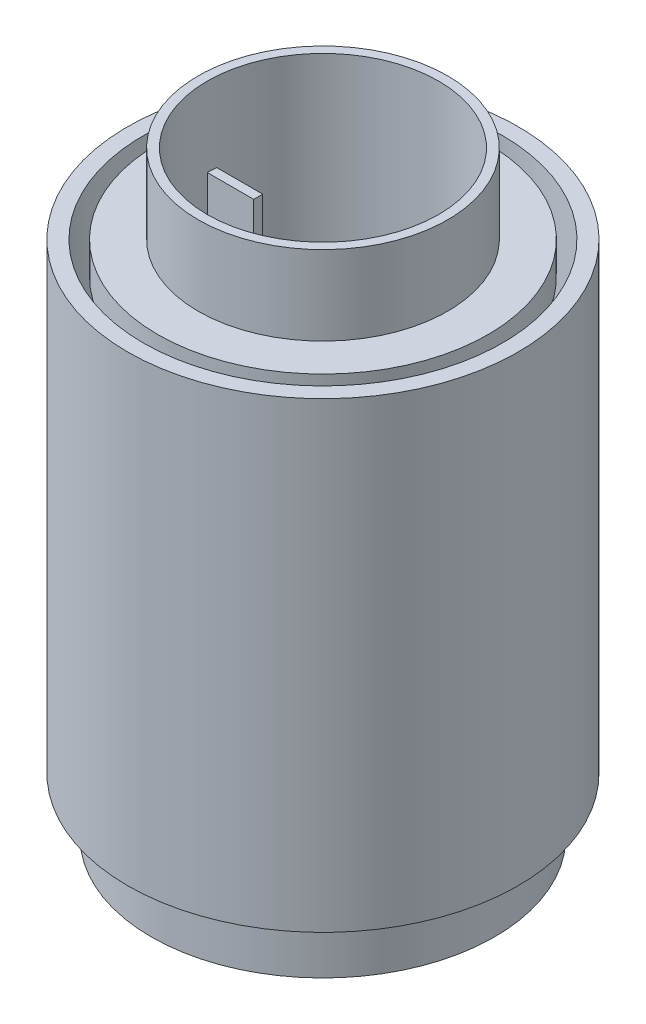
SolidWorks part; units mm, degrees
ref_plane "Alzado" through (0, 0, 0) normal (0, 0, 1) x (1, 0, 0)
ref_plane "Planta" through (0, 0, 0) normal (0, 1, 0) x (1, 0, 0)
ref_plane "Vista lateral" through (0, 0, 0) normal (1, 0, 0) x (0, 0, -1)
sketch "Croquis1" plane through (0, 0, 0) normal (0, 1, 0) x (1, 0, 0)
  circle A0 centre (0, 0) radius 25
  circle A1 centre (0, 0) radius 17.6776
  dimension "D1" = 50
extrude "Saliente-Extruir1" add sketch "Croquis1" along normal blind 5
sketch "Croquis3" plane through (0, 5, 0) normal (0, 1, 0) x (1, 0, 0)
  circle A0 centre (0, 0) radius 17.518
  circle A1 centre (0, 0) radius 25 construction
  circle A2 centre (0, 0) radius 17.6443
  dimension "D1" = 35.0359
extrude "Saliente-Extruir3" add sketch "Croquis3" against normal blind 70 separate body
sketch "Croquis5" plane through (0, 0, 0) normal (0, -1, 0) x (-1, 0, 0)
  circle A0 centre (0, 0) radius 17.518
  circle A1 centre (0, 0) radius 25.75
  circle A2 centre (0, 0) radius 25 construction
  dimension "D1" = 35.0359
  dimension "D2" = 51.5
ref_plane "Plano1" through (0, -65, 0) normal (0, 1, 0) x (1, 0, 0)
sketch "Croquis6" plane through (0, -65, 0) normal (0, 1, 0) x (1, 0, 0)
  circle A0 centre (0, 0) radius 17.518
  circle A1 centre (0, 0) radius 26
  dimension "D1" = 35.0359
  dimension "D2" = 52
extrude "Saliente-Extruir5" add sketch "Croquis6" against normal blind 8.5
sketch "Croquis7" plane through (0, -65, 0) normal (0, 1, 0) x (1, 0, 0)
  line L0 (17.4651, 1.3604) -> (10.4841, 1.3604)
  line L1 (10.4841, 1.3604) -> (10.4841, 0)
  line L2 (10.4841, 0) -> (17.518, 0)
  line L3 (17.518, 0) -> (17.4651, 1.3604)
  line L4 (-17.518, 0) -> (-10.4841, 0)
  line L5 (-10.4841, 0) -> (-10.4841, 1.3604)
  line L6 (-10.4841, 1.3604) -> (-17.4651, 1.3604)
  line L7 (-17.4651, 1.3604) -> (-17.518, 0)
  circle A0 centre (0, 0) radius 17.518 construction
  point P9 (0, 0)
  dimension "D1" = 10.4841
  dimension "D2" = 17.4651
extrude "Saliente-Extruir6" add sketch "Croquis7" along normal through all separate body
sketch "Croquis8" plane through (0, -65, 0) normal (0, 1, 0) x (1, 0, 0)
  circle A0 centre (0, 0) radius 17.518
  circle A1 centre (0, 0) radius 19.0275
  dimension "D1" = 35.0359
  dimension "D2" = 38.0551
extrude "Saliente-Extruir7" add sketch "Croquis8" against normal blind 9
ref_plane "Plano2" through (0, 5, 0) normal (0, 1, 0) x (1, 0, 0)
sketch "Croquis10" plane through (0, 5, 0) normal (0, 1, 0) x (1, 0, 0)
  circle A0 centre (0, 0) radius 17.518
  circle A1 centre (0, 0) radius 18.8887
  circle A2 centre (0, 0) radius 25 construction
  dimension "D1" = 35.0359
  dimension "D2" = 37.7774
extrude "Saliente-Extruir8" add sketch "Croquis10" along normal blind 12
sketch "Croquis11" plane through (0, -65, 0) normal (0, 1, 0) x (1, 0, 0)
  circle A0 centre (0, 0) radius 27.2032
  circle A1 centre (0, 0) radius 29.5668
  dimension "D1" = 54.4064
  dimension "D2" = 59.1336
extrude "Saliente-Extruir9" add sketch "Croquis11" along normal blind 70 separate body
